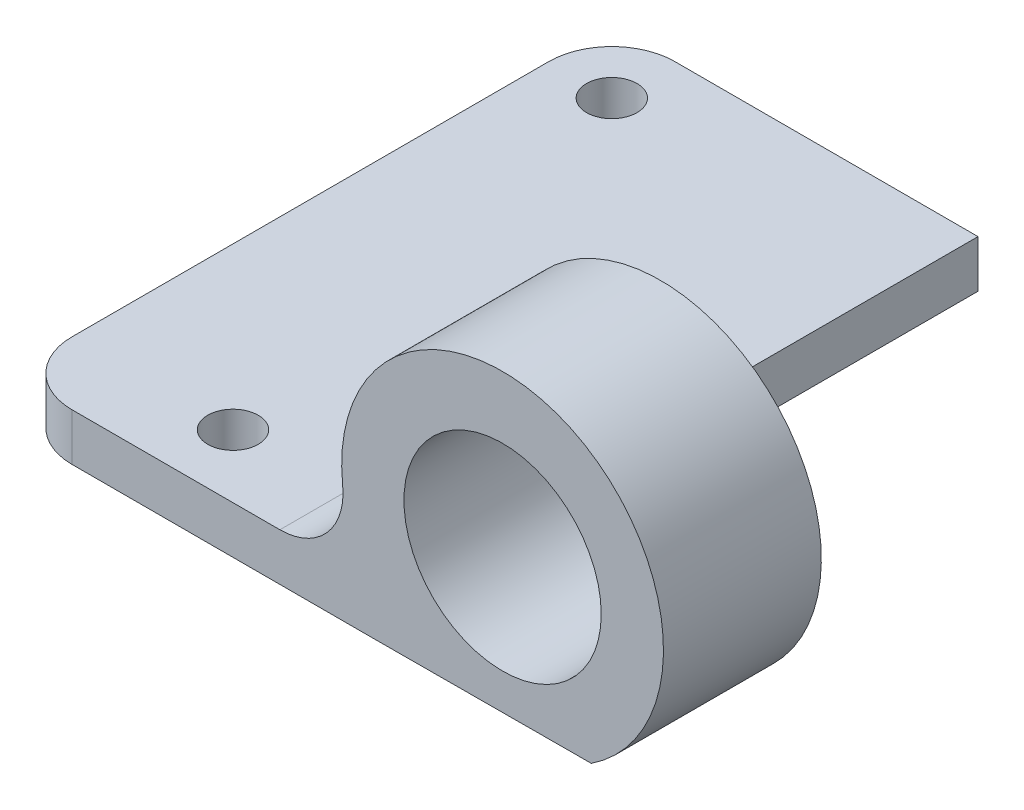
SolidWorks part; units mm, degrees
ref_plane "Front Plane" through (0, 0, 0) normal (0, 0, 1) x (1, 0, 0)
ref_plane "Top Plane" through (0, 0, 0) normal (0, 1, 0) x (1, 0, 0)
ref_plane "Right Plane" through (0, 0, 0) normal (1, 0, 0) x (0, 0, -1)
sketch "Sketch1" plane through (0, 0, 0) normal (0, 1, 0) x (1, 0, 0)
  line L1 (-3.9914, 4.3795) -> (19.2086, 4.3795)
  line L2 (-3.9914, 4.3795) -> (-3.9914, -33.8205)
  line L3 (-3.9914, -33.8205) -> (19.2086, -33.8205)
  line L4 (19.2086, 4.3795) -> (19.2086, -33.8205)
  circle A0 centre (0.0086, 0.3795) radius 1.6
  circle A1 centre (6.2086, -29.8205) radius 1.6
  dimension "D1" = 6.2
  dimension "D2" = 30.2
  dimension "D3" = 3.2
  dimension "D4" = 4
  dimension "D5" = 4
  dimension "D6" = 4
  dimension "D7" = 13
extrude "Boss-Extrude1" add sketch "Sketch1" along normal blind 3
fillet "Fillet1" radius 4 2 edges at (-3.9914, 1.5, 33.8205) (-3.9914, 1.5, -4.3795)
sketch "Sketch2" plane through (0, 0, 33.8205) normal (0, 0, 1) x (1, 0, 0)
  line L0 (0.0086, 3) -> (19.2086, 3) construction
  line L1 (19.2086, 3) -> (19.2086, 0) construction
  line L2 (19.2086, 0) -> (32.9111, 0.0473)
  line L3 (19.2086, 0) -> (19.2086, 2.3353)
  circle A0 centre (27.2886, 8.55) radius 6.25
  arc A1 (32.9111, 0.0473) -> (19.2086, 2.3353) centre (27.2886, 8.55) ccw
  dimension "D1" = 5.55
  dimension "D3" = 12.5
  dimension "D2" = 8.08
extrude "Boss-Extrude2" add sketch "Sketch2" against normal blind 10
fillet "Fillet2" radius 4 1 edges at (18.7383, 3, 28.8205)
